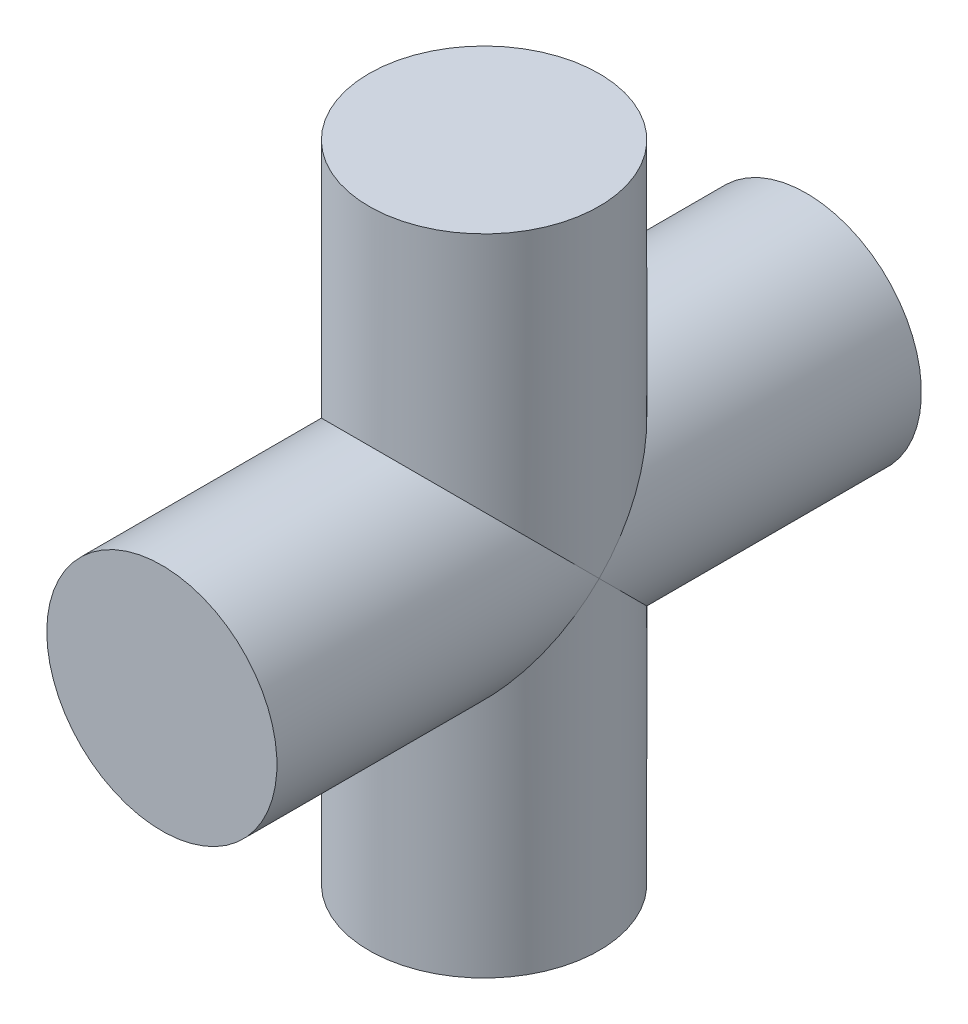
SolidWorks part; units mm, degrees
ref_plane "Front Plane" through (0, 0, 0) normal (0, 0, 1) x (1, 0, 0)
ref_plane "Top Plane" through (0, 0, 0) normal (0, 1, 0) x (1, 0, 0)
ref_plane "Right Plane" through (0, 0, 0) normal (1, 0, 0) x (0, 0, -1)
sketch "Sketch1" plane through (0, 0, 0) normal (0, 0, 1) x (1, 0, 0)
  line L1 (-7.5, 21) -> (0, 21)
  line L2 (-7.5, 21) -> (-7.5, -21)
  line L3 (-7.5, -21) -> (0, -21)
  line L4 (0, 21) -> (0, -21)
  dimension "D1" = 7.5
  dimension "D2" = 42
  dimension "D3" = 21
revolve "Revolve1" add sketch "Sketch1" angle 360 about L4
sketch "Sketch2" plane through (0, 0, 0) normal (0, 1, 0) x (1, 0, 0)
  line L1 (-7.5, 21) -> (0, 21)
  line L2 (-7.5, 21) -> (-7.5, -21)
  line L3 (-7.5, -21) -> (0, -21)
  line L4 (0, 21) -> (0, -21)
  dimension "D1" = 42
  dimension "D2" = 21
  dimension "D3" = 7.5
revolve "Revolve2" add sketch "Sketch2" angle 360 about L4
equation "\"D3@Sketch1\" = \"D2@Sketch1\"/2"
equation "\"D2@Sketch2\" = \"D1@Sketch2\"/2"
